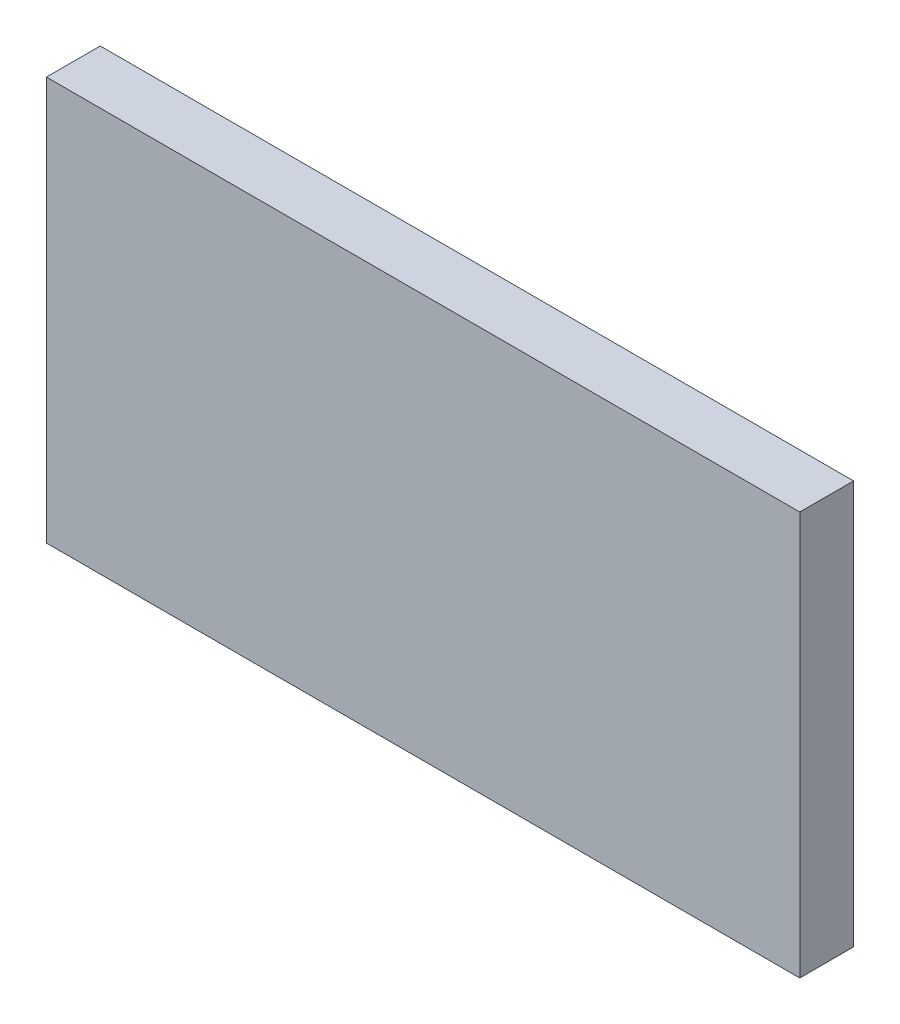
SolidWorks part; units mm, degrees
ref_plane "Alzado" through (0, 0, 0) normal (0, 0, 1) x (1, 0, 0)
ref_plane "Planta" through (0, 0, 0) normal (0, 1, 0) x (1, 0, 0)
ref_plane "Vista lateral" through (0, 0, 0) normal (1, 0, 0) x (0, 0, -1)
sketch "Croquis1" plane through (0, 0, 0) normal (0, 0, 1) x (1, 0, 0)
  line L1 (-166.5844, 89.7479) -> (113.4156, 89.7479)
  line L2 (-166.5844, 89.7479) -> (-166.5844, -60.2521)
  line L3 (-166.5844, -60.2521) -> (113.4156, -60.2521)
  line L4 (113.4156, 89.7479) -> (113.4156, -60.2521)
  dimension "D1" = 280
  dimension "D2" = 150
extrude "Saliente-Extruir1" add sketch "Croquis1" along normal blind 20
